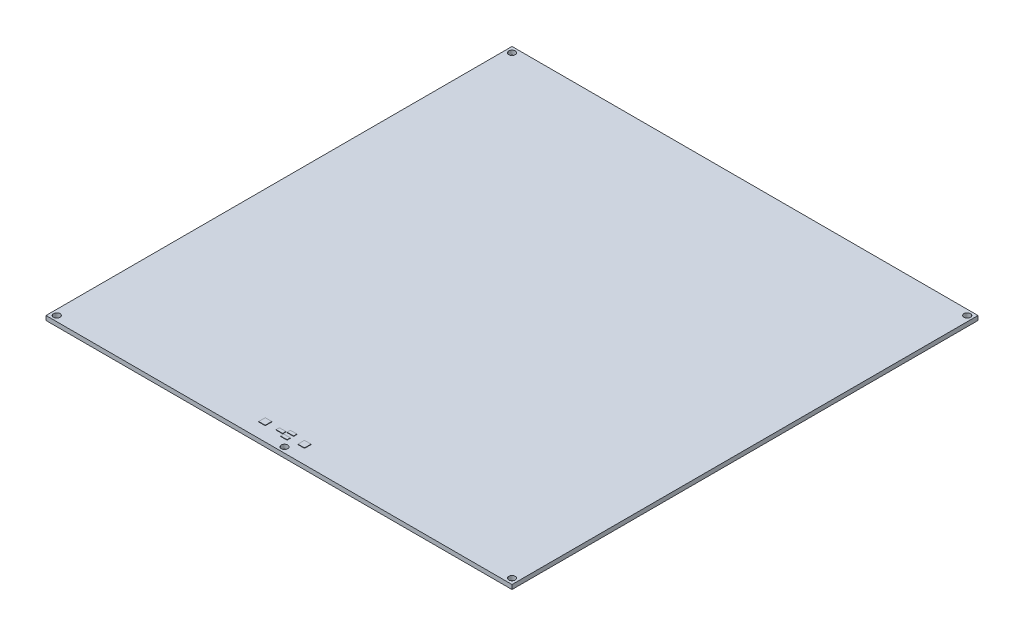
SolidWorks part; units mm, degrees
ref_plane "Alzado" through (0, 0, 0) normal (0, 0, 1) x (1, 0, 0)
ref_plane "Planta" through (0, 0, 0) normal (0, 1, 0) x (1, 0, 0)
ref_plane "Vista lateral" through (0, 0, 0) normal (1, 0, 0) x (0, 0, -1)
ref_plane "Plano1" through (0, 2, 0) normal (0, 1, 0) x (1, 0, 0)
sketch "Croquis1" plane through (0, 2, 0) normal (0, 1, 0) x (1, 0, 0)
  line L0 (-107, 107) -> (-107, -107)
  line L1 (-107, -107) -> (107, -107)
  line L2 (107, -107) -> (107, 107)
  line L3 (107, 107) -> (-107, 107)
extrude "Saliente-Extruir1" add sketch "Croquis1" against normal blind 2
sketch "Croquis2" plane through (0, 2, 0) normal (0, 1, 0) x (-1, 0, 0)
  line L0 (-2.2, 97.5) -> (-5.2, 97.5)
  line L1 (-5.2, 97.5) -> (-5.2, 100.5)
  line L2 (-5.2, 100.5) -> (-2.2, 100.5)
  line L3 (-2.2, 100.5) -> (-2.2, 97.5)
extrude "Saliente-Extruir2" add sketch "Croquis2" along normal blind 0.2
sketch "Croquis3" plane through (0, 2, 0) normal (0, 1, 0) x (-1, 0, 0)
  line L0 (15.8, 97.5) -> (12.8, 97.5)
  line L1 (12.8, 97.5) -> (12.8, 100.5)
  line L2 (12.8, 100.5) -> (15.8, 100.5)
  line L3 (15.8, 100.5) -> (15.8, 97.5)
extrude "Saliente-Extruir3" add sketch "Croquis3" along normal blind 0.2
sketch "Croquis4" plane through (0, 2, 0) normal (0, 1, 0) x (-1, 0, 0)
  line L0 (5.55, 98.25) -> (5.55, 99.75)
  line L1 (5.55, 99.75) -> (8.55, 99.75)
  line L2 (8.55, 99.75) -> (8.55, 98.25)
  line L3 (8.55, 98.25) -> (5.55, 98.25)
extrude "Saliente-Extruir4" add sketch "Croquis4" along normal blind 0.2
sketch "Croquis5" plane through (0, 2, 0) normal (0, 1, 0) x (-1, 0, 0)
  line L0 (2.05, 98.25) -> (5.05, 98.25)
  line L1 (5.05, 98.25) -> (5.05, 96.75)
  line L2 (5.05, 96.75) -> (2.05, 96.75)
  line L3 (2.05, 96.75) -> (2.05, 98.25)
extrude "Saliente-Extruir5" add sketch "Croquis5" along normal blind 0.2
sketch "Croquis6" plane through (0, 2, 0) normal (0, 1, 0) x (-1, 0, 0)
  line L0 (2.05, 101.25) -> (5.05, 101.25)
  line L1 (5.05, 101.25) -> (5.05, 99.75)
  line L2 (5.05, 99.75) -> (2.05, 99.75)
  line L3 (2.05, 99.75) -> (2.05, 101.25)
extrude "Saliente-Extruir6" add sketch "Croquis6" along normal blind 0.2
hole_wizard "Diámetro de taladro Ø3.0 (3)1" positions "Croquis8" profile "Croquis7" hole size "Ø3.0" standard "Ansi Metric" end condition through all
sketch "Croquis8" plane through (0, 2, 0) normal (0, 1, 0) x (1, 0, 0)
  point P0 (104.5251, 104.5251)
  point P1 (-104.5251, -104.5251)
  point P2 (104.4749, -104.4749)
  point P3 (-104.4749, 104.4749)
  point P4 (0, -104.4749)
sketch "Croquis7" plane through (104.5251, 2, -104.5251) normal (1, 0, 0) x (0, 0, 1)
  line L0 (0, 0) -> (0, 2)
  line L1 (0, 2) -> (1.5, 2)
  line L2 (1.5, 2) -> (1.5, 0)
  line L5 (1.5, 0) -> (0, 0)
  line L11 (0, -6.35) -> (0, 107.95) construction
  dimension "Diámetro de taladro hasta el siguiente" = 3
  dimension "Profundidad de taladro hasta el siguiente" = 2
